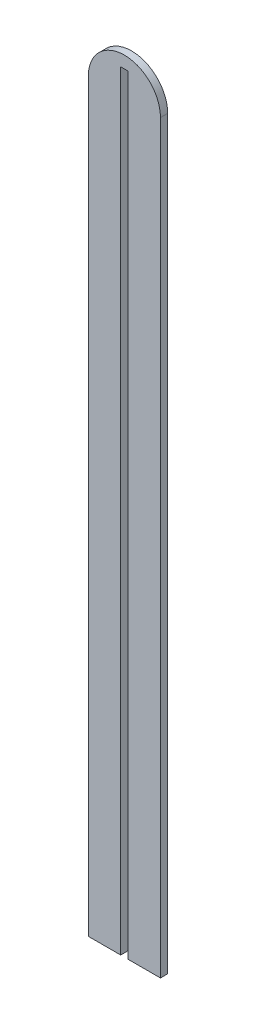
SolidWorks part; units mm, degrees
ref_plane "Front Plane" through (0, 0, 0) normal (0, 0, 1) x (1, 0, 0)
ref_plane "Top Plane" through (0, 0, 0) normal (0, 1, 0) x (1, 0, 0)
ref_plane "Right Plane" through (0, 0, 0) normal (1, 0, 0) x (0, 0, -1)
sketch "Sketch2" plane through (0, 0, 0) normal (0, 0, 1) x (1, 0, 0)
  line L1 (-1.55, -155) -> (1.55, -155)
  line L2 (-15, 155) -> (-15, -155)
  line L3 (-15, -155) -> (15, -155)
  line L4 (15, 155) -> (15, -155)
  line L5 (-15, 155) -> (15, -155) construction
  line L6 (-15, -155) -> (15, 155) construction
  line L7 (-1.55, -155) -> (-1.55, 165)
  line L8 (-1.55, 165) -> (1.55, 165)
  line L9 (1.55, -155) -> (1.55, 165)
  arc A0 (15, 155) -> (-15, 155) centre (0, 155) ccw
  point P0 (0, 0)
  dimension "D3" = 30
  dimension "D1" = 30
  dimension "D2" = 310
  dimension "D4" = 13.45
  dimension "D5" = 13.45
  dimension "D6" = 320
extrude "Boss-Extrude1" add sketch "Sketch2" along normal mid plane 3 contours L4 A0 L2 L3 L7 L8 L9
